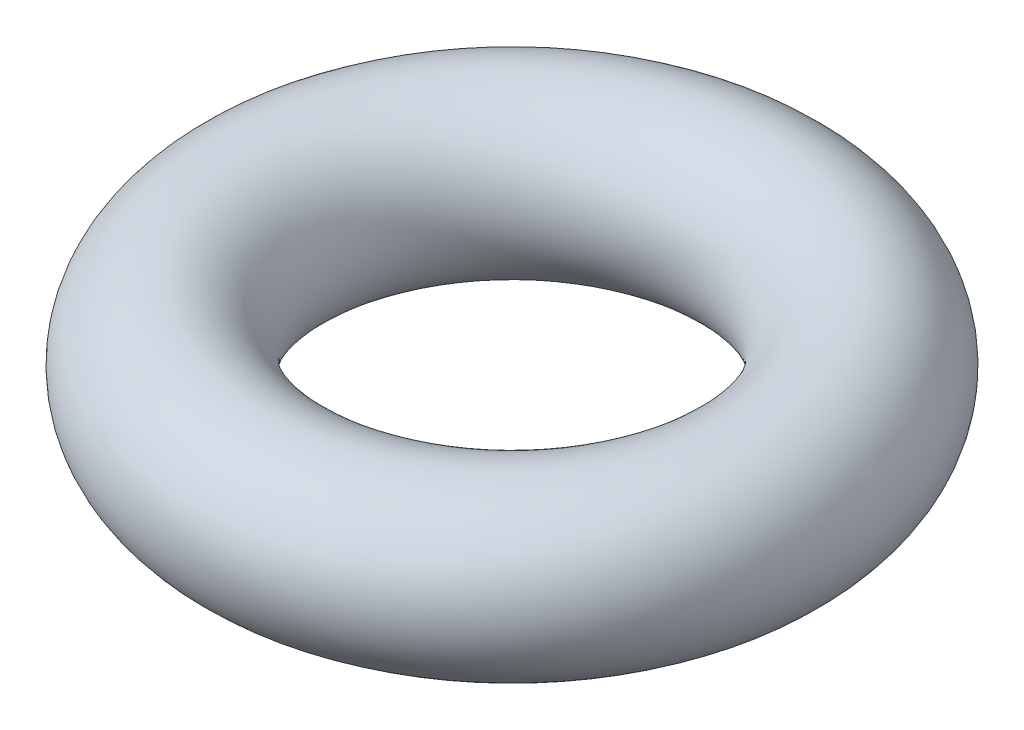
SolidWorks part; units mm, degrees
ref_plane "Front Plane" through (0, 0, 0) normal (0, 0, 1) x (1, 0, 0)
ref_plane "Top Plane" through (0, 0, 0) normal (0, 1, 0) x (1, 0, 0)
ref_plane "Right Plane" through (0, 0, 0) normal (1, 0, 0) x (0, 0, -1)
sketch "Sketch1" plane through (0, 0, 0) normal (0, 0, 1) x (1, 0, 0)
  line L0 (0, 34.9617) -> (0, -47.8526) construction
  circle A0 centre (76.2, 0) radius 25.4
  dimension "D1" = 50.8
  dimension "D2" = 76.2
revolve "Revolve1" add sketch "Sketch1" angle 360 about L0
